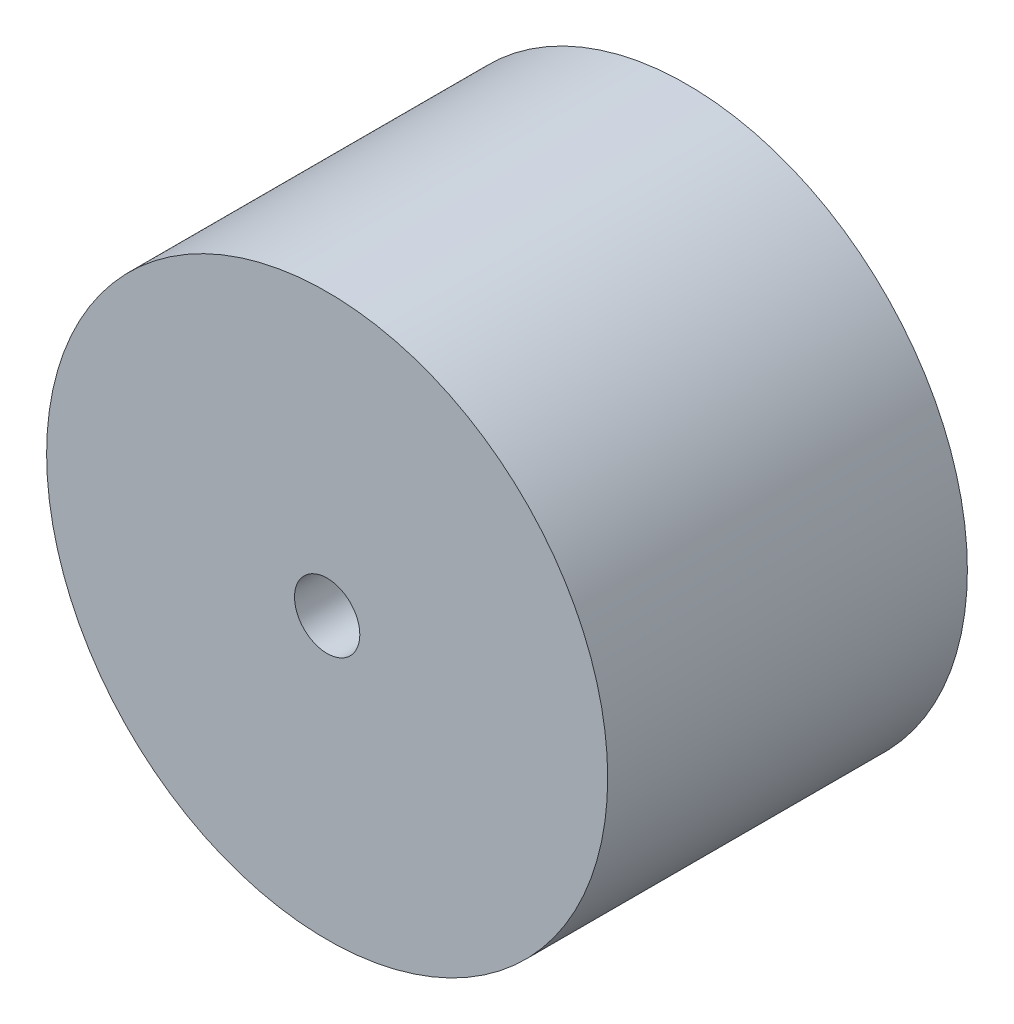
SolidWorks part; units mm, degrees
ref_plane "Front Plane" through (0, 0, 0) normal (0, 0, 1) x (1, 0, 0)
ref_plane "Top Plane" through (0, 0, 0) normal (0, 1, 0) x (1, 0, 0)
ref_plane "Right Plane" through (0, 0, 0) normal (1, 0, 0) x (0, 0, -1)
sketch "Sketch1" plane through (0, 0, 0) normal (0, 0, 1) x (1, 0, 0)
  circle A0 centre (0, 0) radius 3.9
extrude "Boss-Extrude1" add sketch "Sketch1" along normal blind 5
sketch "Sketch2" plane through (0, 0, 5) normal (0, 0, 1) x (1, 0, 0)
  circle A0 centre (0, 0) radius 0.454
extrude "Cut-Extrude1" cut sketch "Sketch2" against normal blind 5
